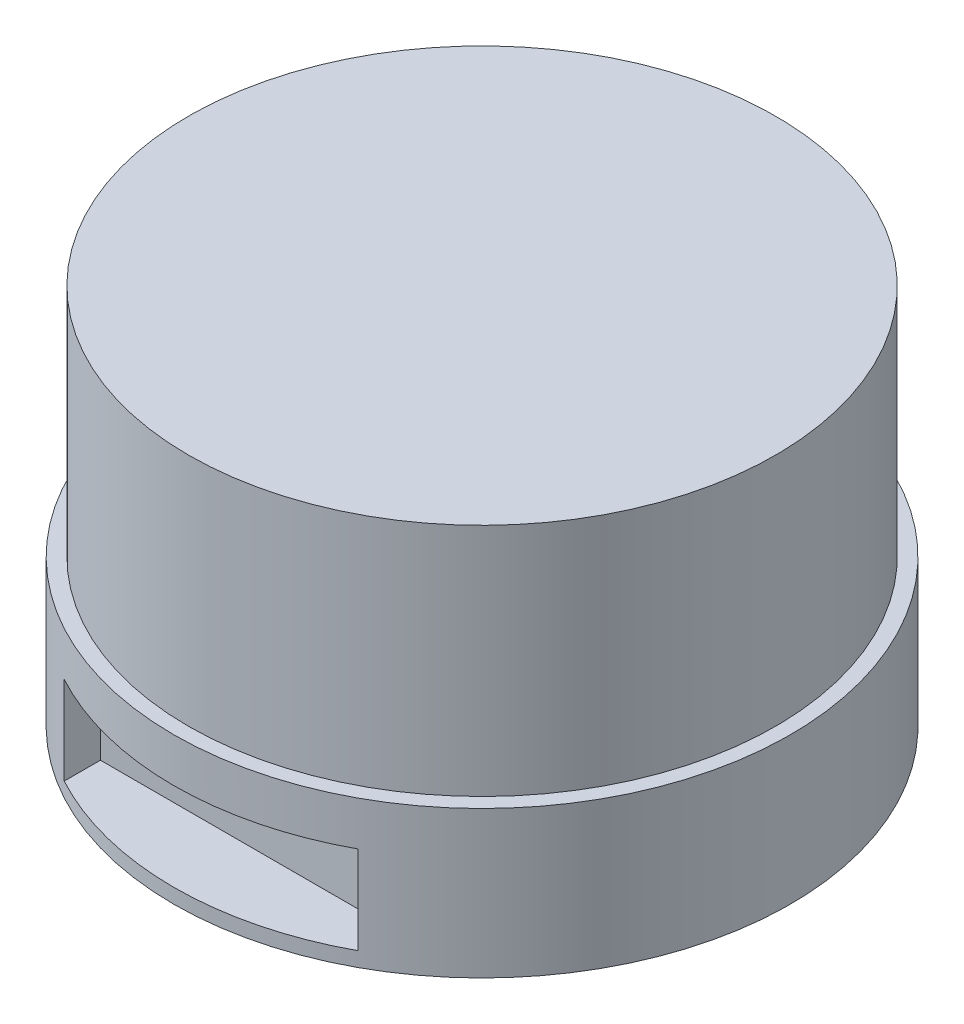
SolidWorks part; units mm, degrees
ref_plane "前视基准面" through (0, 0, 0) normal (0, 0, 1) x (1, 0, 0)
ref_plane "上视基准面" through (0, 0, 0) normal (0, 1, 0) x (1, 0, 0)
ref_plane "右视基准面" through (0, 0, 0) normal (1, 0, 0) x (0, 0, -1)
sketch "草图1" plane through (0, 0, 0) normal (0, 1, 0) x (1, 0, 0)
  circle A0 centre (0, 0) radius 21
  dimension "D1" = 42
extrude "凸台-拉伸1" add sketch "草图1" along normal blind 10
sketch "草图3" plane through (0, 10, 0) normal (0, 1, 0) x (1, 0, 0)
  circle A0 centre (0, 0) radius 21
  dimension "D1" = 42
sketch "草图4" plane through (0, 10, 0) normal (0, 1, 0) x (1, 0, 0)
  circle A0 centre (0, 0) radius 20
  dimension "D1" = 40
extrude "凸台-拉伸3" add sketch "草图4" along normal blind 16
sketch "草图6" plane through (0, 0, 0) normal (0, -1, 0) x (1, 0, 0)
  line L0 (0, 0) -> (0, 21) construction
  line L1 (0, 0) -> (14.8492, 14.8492) construction
  circle A0 centre (0, 0) radius 18 construction
  circle A1 centre (0, 0) radius 21 construction
  circle A2 centre (12.7279, 12.7279) radius 1.5
  circle A3 centre (12.7279, -12.7279) radius 1.5
  circle A4 centre (-12.7279, -12.7279) radius 1.5
  circle A5 centre (-12.7279, 12.7279) radius 1.5
  point P18 (0, 0)
  dimension "D1" = 36
  dimension "D3" = 3
  dimension "D2" = 45
  dimension "D4" = 4
extrude "切除-拉伸1" cut sketch "草图6" against normal blind 4
sketch "草图7" plane through (0, 0, 0) normal (0, -1, 0) x (1, 0, 0)
  circle A0 centre (0, 0) radius 10
  circle A1 centre (0, 0) radius 9
  dimension "D1" = 20
  dimension "D2" = 18
extrude "凸台-拉伸4" add sketch "草图7" along normal blind 1.5
ref_plane "基准面4" through (0, 0, 21) normal (0, 0, 1) x (1, 0, 0)
sketch "草图8" plane through (0, 0, 21) normal (0, 0, 1) x (1, 0, 0)
  line L0 (0, 31.128) -> (0, -11.2174) construction
  line L1 (-10, 1) -> (10, 1)
  line L3 (10, 1) -> (10, 7)
  line L4 (10, 7) -> (-10, 7)
  line L5 (-10, 7) -> (-10, 1)
  line L6 (-21, 0) -> (21, 0) construction
  point P7 (0, 1)
  dimension "D1" = 20
  dimension "D2" = 6
  dimension "D3" = 1
extrude "切除-拉伸2" cut sketch "草图8" against normal blind 5
